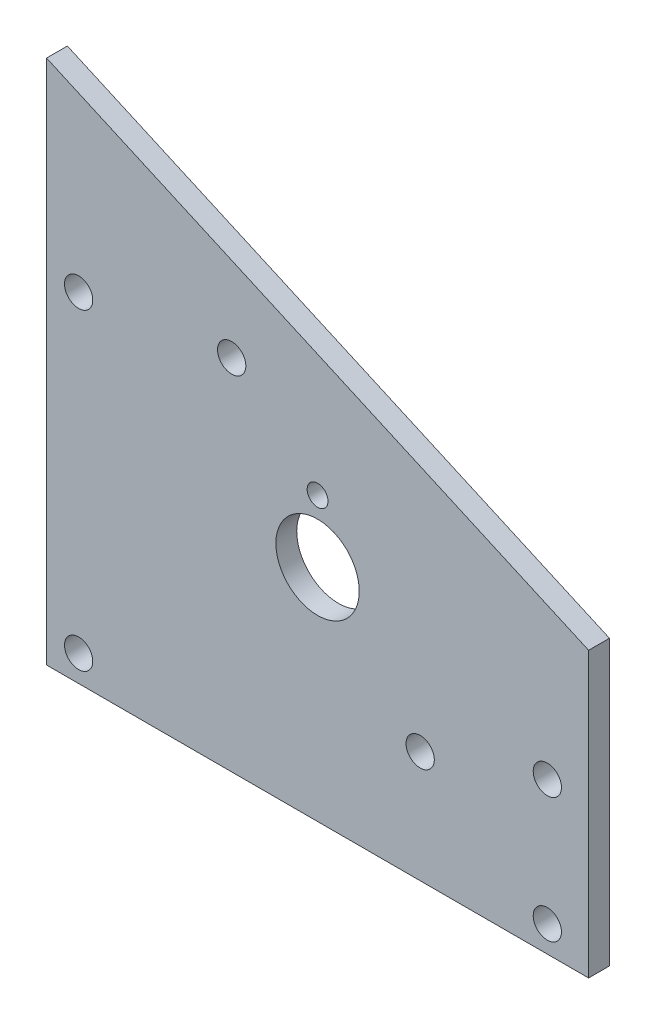
SolidWorks part; units mm, degrees
ref_plane "Front Plane" through (0, 0, 0) normal (0, 0, 1) x (1, 0, 0)
ref_plane "Top Plane" through (0, 0, 0) normal (0, 1, 0) x (1, 0, 0)
ref_plane "Right Plane" through (0, 0, 0) normal (1, 0, 0) x (0, 0, -1)
sketch "Sketch1" plane through (0, 0, 0) normal (0, 0, 1) x (1, 0, 0)
  line L16 (49.022, 13.462) -> (57.658, 13.462)
  line L17 (62.738, 8.382) -> (62.738, 0)
  line L18 (62.738, 0) -> (82.55, 0)
  line L19 (82.55, 0) -> (82.55, 58.42)
  line L20 (82.55, 58.42) -> (0, 95.25)
  line L21 (0, 95.25) -> (0, 0)
  line L22 (0, 0) -> (43.942, 0)
  line L23 (43.942, 0) -> (43.942, 8.382)
  arc A4 (62.738, 8.382) -> (57.658, 13.462) centre (57.658, 8.382) ccw
  arc A5 (49.022, 13.462) -> (43.942, 8.382) centre (49.022, 8.382) ccw
extrude "Boss-Extrude1" add sketch "Sketch1" against normal blind 3.175
hole_wizard "#6 Clearance Hole1" positions "Sketch3" profile "Sketch2" hole size "#6" standard "ANSI Inch" end condition through all
sketch "Sketch3" plane through (0, 0, -3.175) normal (0, 0, -1) x (-1, 0, 0)
  point P0 (-4.8895, 17.4625)
  point P4 (-4.8895, 65.0875)
  point P7 (-76.2635, 36.5125)
  point P10 (-76.2635, 17.4625)
  point P14 (-28.194, 68.072)
  point P17 (-56.896, 30.48)
sketch "Sketch2" plane through (4.8895, 17.4625, -3.175) normal (1, 0, 0) x (0, 1, 0)
  line L0 (0, 0) -> (0, 3.175)
  line L1 (0, 3.175) -> (2.1526, 3.175)
  line L2 (2.1526, 3.175) -> (2.1526, 0)
  line L5 (2.1526, 0) -> (0, 0)
  line L11 (0, -6.35) -> (0, 107.95) construction
  dimension "Thru Hole Dia." = 4.3053
  dimension "Thru Hole Depth" = 3.175
hole_wizard "1/2 (0.5) Diameter Hole1" positions "Sketch5" profile "Sketch4" hole size "1/2" standard "ANSI Inch" end condition through all
sketch "Sketch5" plane through (0, 0, -3.175) normal (0, 0, -1) x (-1, 0, 0)
  point P0 (-41.275, 46.99)
sketch "Sketch4" plane through (41.275, 46.99, -3.175) normal (1, 0, 0) x (0, 1, 0)
  line L0 (0, 0) -> (0, 3.175)
  line L1 (0, 3.175) -> (6.35, 3.175)
  line L2 (6.35, 3.175) -> (6.35, 0)
  line L5 (6.35, 0) -> (0, 0)
  line L11 (0, -6.35) -> (0, 107.95) construction
  dimension "Thru Hole Dia." = 12.7
  dimension "Thru Hole Depth" = 3.175
hole_wizard "1/8 (0.125) Diameter Hole1" positions "Sketch7" profile "Sketch6" hole size "1/8" standard "ANSI Inch" end condition through all
sketch "Sketch7" plane through (0, 0, 0) normal (0, 0, 1) x (1, 0, 0)
  point P0 (41.275, 56.4889)
sketch "Sketch6" plane through (41.275, 56.4889, 0) normal (1, 0, 0) x (0, -1, 0)
  line L0 (0, 0) -> (0, 3.175)
  line L1 (0, 3.175) -> (1.5875, 3.175)
  line L2 (1.5875, 3.175) -> (1.5875, 0)
  line L5 (1.5875, 0) -> (0, 0)
  line L11 (0, -6.35) -> (0, 107.95) construction
  dimension "Thru Hole Dia." = 3.175
  dimension "Thru Hole Depth" = 3.175
sketch "Sketch9" plane through (0, 0, 0) normal (0, 0, 1) x (1, 0, 0)
  line L1 (82.55, 58.42) -> (0, 95.25) construction
  line L2 (81.9032, 56.9702) -> (-0.6468, 93.8002)
  line L3 (82.55, 56.6817) -> (0, 93.5117)
  line L4 (82.55, 58.42) -> (0, 95.25)
  line L5 (82.55, 0) -> (82.55, 58.42) construction
  line L6 (0, 95.25) -> (0, 0) construction
  line L7 (0, 95.25) -> (0, 93.5117)
  line L8 (82.55, 58.42) -> (82.55, 56.6817)
  dimension "D1" = 1.5875
extrude "Cut-Extrude1" cut sketch "Sketch9" against normal through all
sketch "Sketch10" plane through (0, 0, 0) normal (0, 0, 1) x (1, 0, 0)
  line L0 (0, 93.5117) -> (0, 0) construction
  line L1 (82.55, 0) -> (0, 0)
  line L2 (82.55, 0) -> (82.55, 13.462)
  line L3 (82.55, 13.462) -> (0, 13.462)
  line L4 (0, 0) -> (0, 13.462)
  line L5 (49.022, 13.462) -> (57.658, 13.462) construction
extrude "Cut-Extrude2" cut sketch "Sketch10" against normal through all
